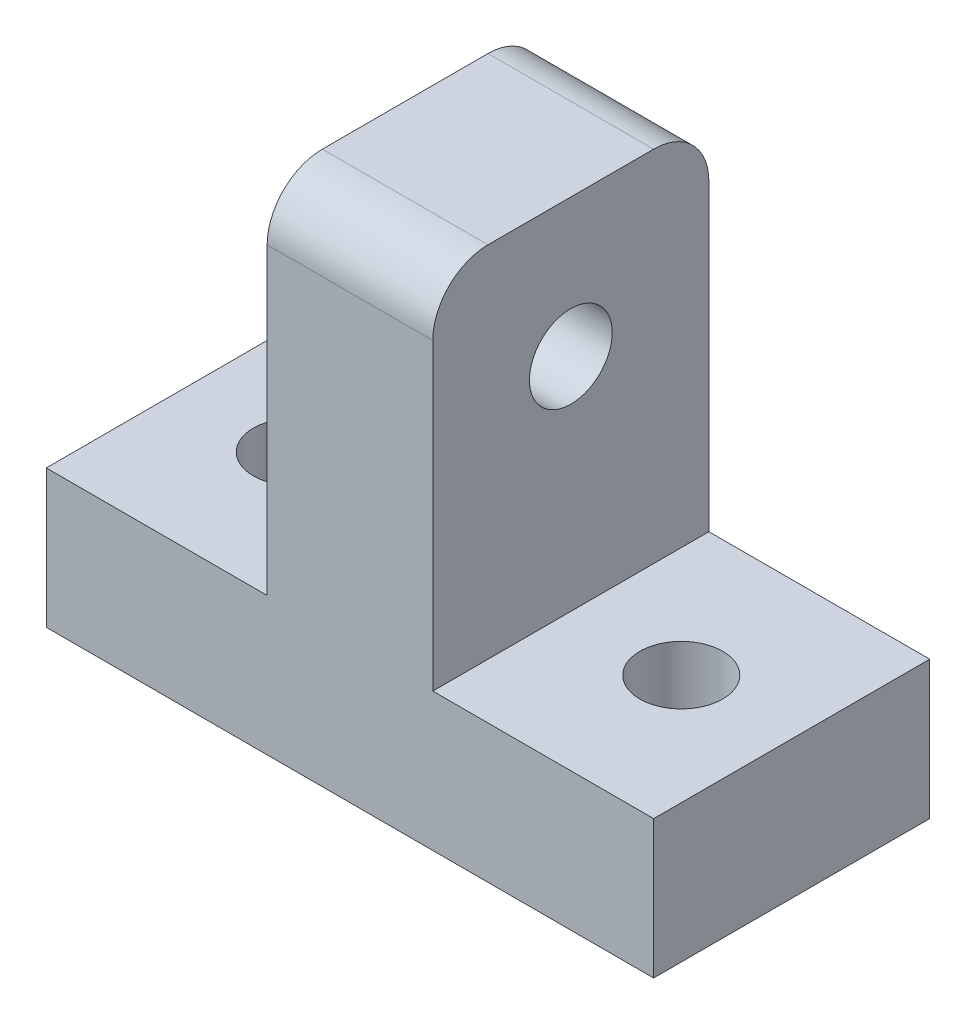
SolidWorks part; units mm, degrees
ref_plane "Front" through (0, 0, 0) normal (0, 0, 1) x (1, 0, 0)
ref_plane "Top" through (0, 0, 0) normal (0, 1, 0) x (1, 0, 0)
ref_plane "Right" through (0, 0, 0) normal (1, 0, 0) x (0, 0, -1)
sketch "Sketch1" plane through (0, 0, 0) normal (0, 1, 0) x (1, 0, 0)
  line L1 (-11, -5) -> (11, -5)
  line L2 (-11, -5) -> (-11, 5)
  line L3 (-11, 5) -> (11, 5)
  line L4 (11, -5) -> (11, 5)
  line L5 (-11, -5) -> (11, 5) construction
  line L6 (-11, 5) -> (11, -5) construction
  circle A2 centre (-7, 0) radius 1.5
  circle A3 centre (7, 0) radius 1.5
  point P0 (0, 0)
  dimension "D3" = 3
  dimension "D4" = 3
  dimension "D5" = 4
  dimension "D6" = 4
  dimension "D1" = 10
  dimension "D2" = 22
extrude "Boss-Extrude1" add sketch "Sketch1" along normal blind 5
sketch "Sketch4" plane through (0, 5, 0) normal (0, 1, 0) x (1, 0, 0)
  line L0 (11, 5) -> (-11, 5) construction
  line L1 (-3, -5) -> (3, -5)
  line L2 (-3, -5) -> (-3, 5)
  line L3 (-3, 5) -> (3, 5)
  line L4 (3, -5) -> (3, 5)
  line L5 (-3, -5) -> (3, 5) construction
  line L6 (-3, 5) -> (3, -5) construction
  circle A0 centre (-7, 0) radius 1.5 construction
  point P0 (0, 0)
  dimension "D1" = 4
extrude "Boss-Extrude3" add sketch "Sketch4" along normal blind 13
sketch "Sketch5" plane through (3, 0, 0) normal (1, 0, 0) x (0, 0, -1)
  line L0 (0, 18) -> (0, 5) construction
  line L1 (5, 18) -> (-5, 18) construction
  line L2 (5, 5) -> (-5, 5) construction
  circle A0 centre (0, 13) radius 1.5
  dimension "D1" = 3
  dimension "D2" = 8
extrude "Cut-Extrude1" cut sketch "Sketch5" against normal up to next
fillet "Fillet1" radius 2 2 edges at (0, 18, -5) (0, 18, 5)
